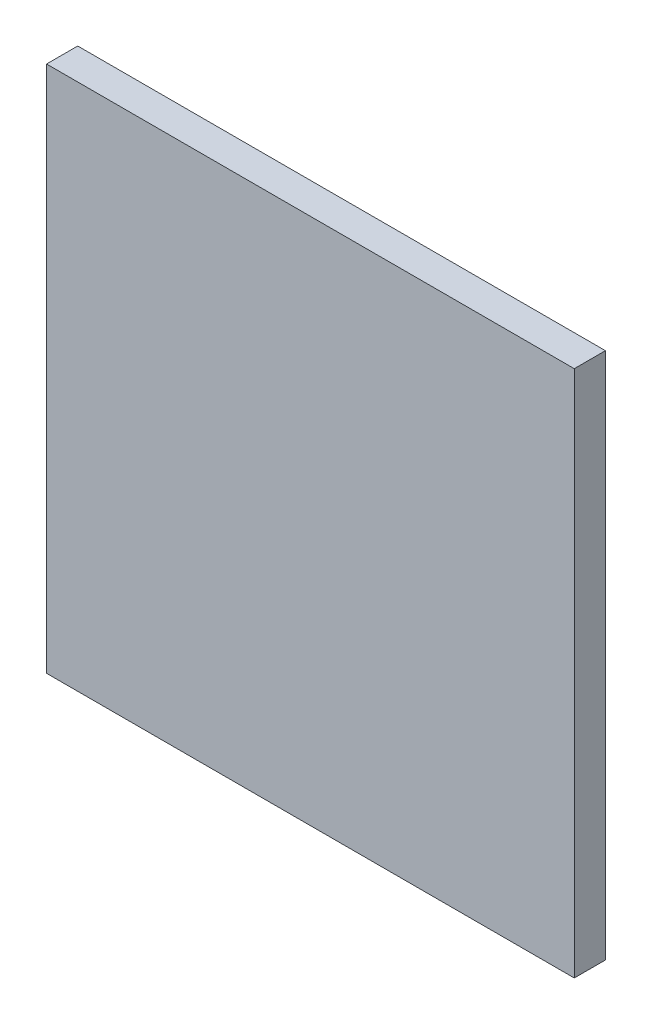
SolidWorks part; units mm, degrees
ref_plane "Front Plane" through (0, 0, 0) normal (0, 0, 1) x (1, 0, 0)
ref_plane "Top Plane" through (0, 0, 0) normal (0, 1, 0) x (1, 0, 0)
ref_plane "Right Plane" through (0, 0, 0) normal (1, 0, 0) x (0, 0, -1)
sketch "Sketch1" plane through (0, 0, 0) normal (0, 0, 1) x (1, 0, 0)
  line L1 (-50.8, -50.8) -> (50.8, -50.8)
  line L2 (-50.8, -50.8) -> (-50.8, 50.8)
  line L3 (-50.8, 50.8) -> (50.8, 50.8)
  line L4 (50.8, -50.8) -> (50.8, 50.8)
  line L5 (-50.8, -50.8) -> (50.8, 50.8) construction
  line L6 (-50.8, 50.8) -> (50.8, -50.8) construction
  point P0 (0, 0)
extrude "Boss-Extrude2" add sketch "Sketch1" along normal blind 6
